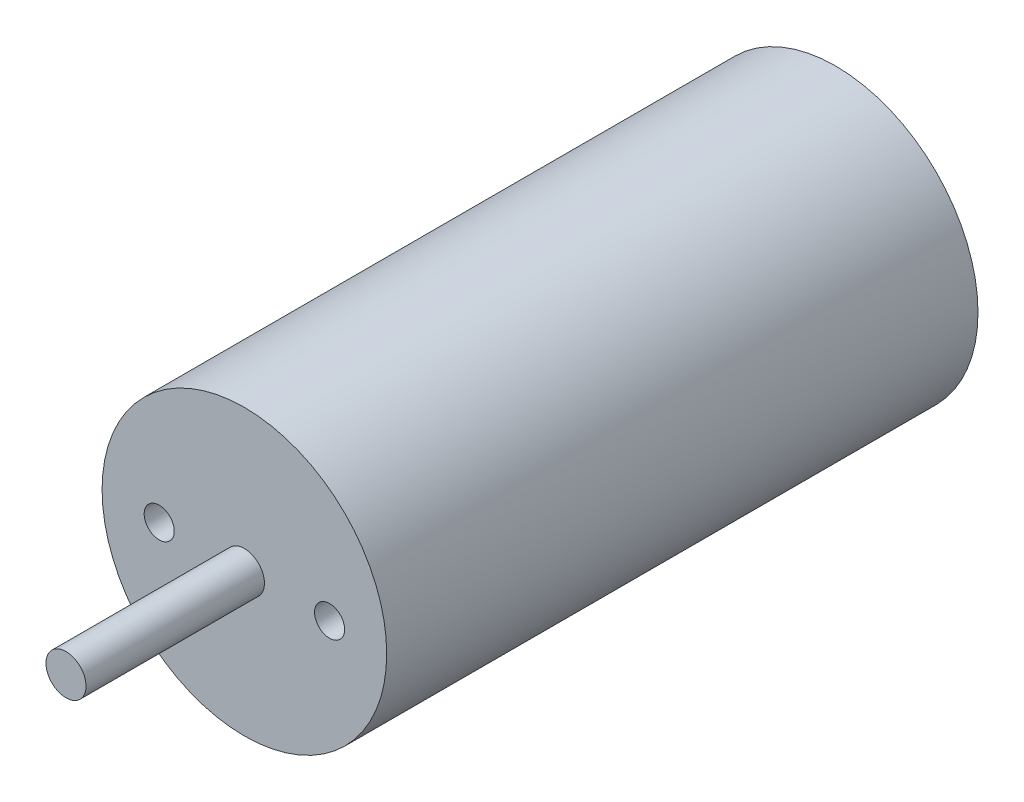
SolidWorks part; units mm, degrees
ref_plane "Front Plane" through (0, 0, 0) normal (0, 0, 1) x (1, 0, 0)
ref_plane "Top Plane" through (0, 0, 0) normal (0, 1, 0) x (1, 0, 0)
ref_plane "Right Plane" through (0, 0, 0) normal (1, 0, 0) x (0, 0, -1)
sketch "Sketch1" plane through (0, 0, 0) normal (0, 0, 1) x (1, 0, 0)
  circle A0 centre (0, 0) radius 14.2
  dimension "D1" = 28.4
extrude "Boss-Extrude1" add sketch "Sketch1" along normal blind 59
sketch "Sketch2" plane through (0, 0, 59) normal (0, 0, 1) x (1, 0, 0)
  circle A0 centre (0, 0) radius 2
  dimension "D1" = 4
extrude "Boss-Extrude2" add sketch "Sketch2" along normal blind 17.8
sketch "Sketch3" plane through (0, 0, 59) normal (0, 0, 1) x (1, 0, 0)
  line L0 (-14.2, 0) -> (14.2, 0) construction
  circle A0 centre (0, 0) radius 14.2 construction
  circle A1 centre (0, 0) radius 8.5 construction
  circle A2 centre (-8.5, 0) radius 1.5
  circle A3 centre (8.5, 0) radius 1.5
  dimension "D1" = 17
  dimension "D2" = 3
  dimension "D3" = 3
extrude "Cut-Extrude1" cut sketch "Sketch3" against normal blind 4.3942
